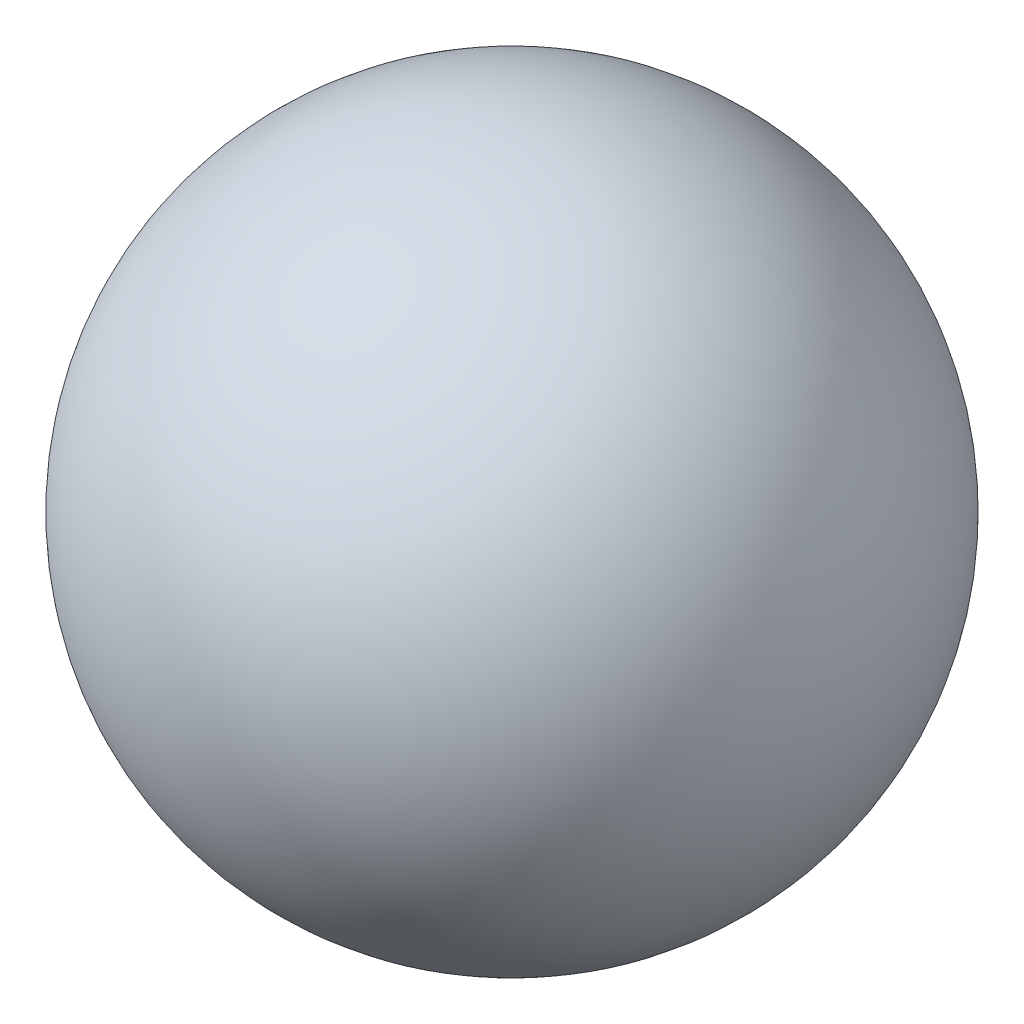
SolidWorks part; units mm, degrees
material "Простая углеродистая сталь"
ref_plane "Front" through (0, 0, 0) normal (0, 0, 1) x (1, 0, 0)
ref_plane "Top" through (0, 0, 0) normal (0, 1, 0) x (1, 0, 0)
ref_plane "Right" through (0, 0, 0) normal (1, 0, 0) x (0, 0, -1)
sketch "Эскиз1" plane through (0, 0, 0) normal (0, 0, 1) x (1, 0, 0)
  line L0 (0, 0) -> (0, 7) construction
  line L1 (0, 7) -> (0, -7)
  arc A0 (0, 7) -> (0, -7) centre (0, 0) ccw
  dimension "D1" = 7
revolve "Повернуть1" add sketch "Эскиз1" angle 360 about L0
